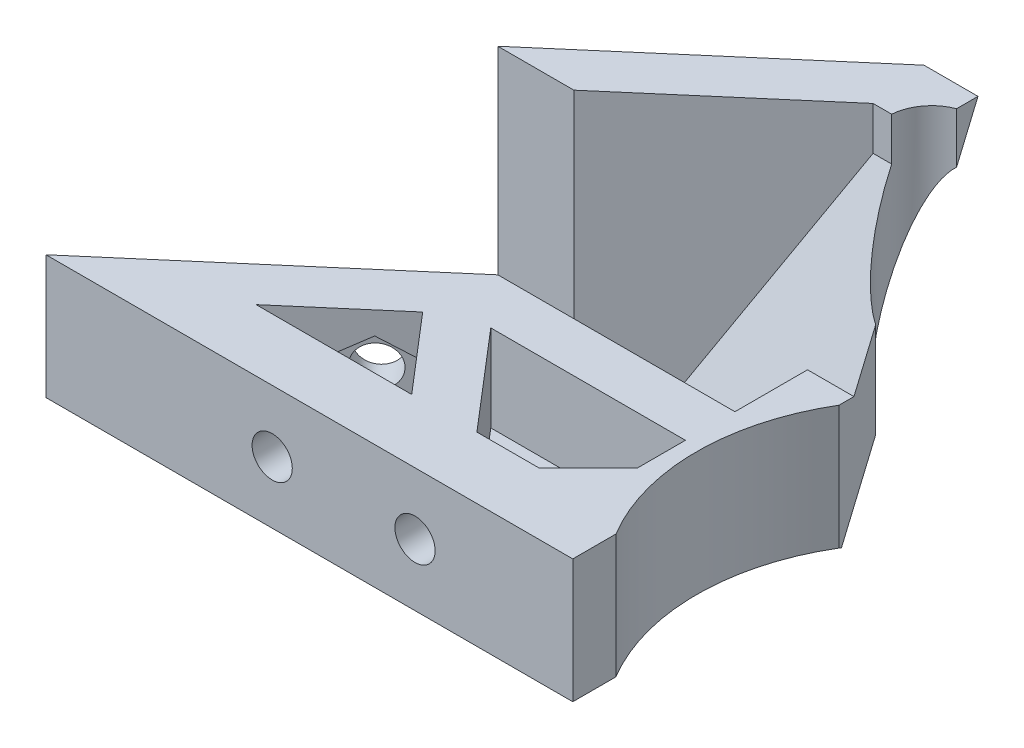
SolidWorks part; units mm, degrees
ref_plane "Alzado" through (0, 0, 0) normal (0, 0, 1) x (1, 0, 0)
ref_plane "Planta" through (0, 0, 0) normal (0, 1, 0) x (1, 0, 0)
ref_plane "Vista lateral" through (0, 0, 0) normal (1, 0, 0) x (0, 0, -1)
sketch "Croquis1" plane through (0, 0, 0) normal (0, 1, 0) x (1, 0, 0)
  line L0 (0, 20) -> (0, -20) construction
  line L1 (-20, 20) -> (20, 20)
  line L2 (-20, 20) -> (-20, -20)
  line L3 (-20, -20) -> (20, -20)
  line L4 (20, 20) -> (20, -20)
  line L5 (-20, 20) -> (20, -20) construction
  line L6 (-20, -20) -> (20, 20) construction
  line L7 (-20, -4.25) -> (-30, -7.25)
  line L8 (-30, -7.25) -> (-30, -15.25)
  line L9 (-30, -15.25) -> (30, -15.25)
  line L10 (20, -4.25) -> (30, -7.25)
  line L11 (30, -7.25) -> (30, -15.25)
  circle A0 centre (-15, 15) radius 2.125
  circle A1 centre (15, 15) radius 2.125
  circle A4 centre (0, 0) radius 15.25
  circle A5 centre (-15, -15) radius 2.125 [skipped]
  circle A6 centre (15, -15) radius 2.125 [skipped]
  point P0 (0, 0)
  point P25 (0, -15.25)
  dimension "D3" = 4.25
  dimension "D7" = 30.5
  dimension "D1" = 40
  dimension "D2" = 40
  dimension "D4" = 5
  dimension "D5" = 2
  dimension "D8" = 8
  dimension "D9" = 10
  dimension "D10" = 15.25
  dimension "D12" = 3
  dimension "D6" = 2
extrude "Soporte caja reductora" add sketch "Croquis1" against normal blind 20
sketch "Croquis3" plane through (0, 0, 15.25) normal (0, 0, 1) x (1, 0, 0)
  line L3 (-20, -20) -> (-20, 0) construction
  circle A0 centre (-23.5, -10) radius 2.125
  circle A1 centre (23.5, -10) radius 2.125
  dimension "D1" = 4.25
  dimension "D2" = 3.5
extrude "Cortar-Extruir1" cut sketch "Croquis3" against normal through all
fillet "Redondeo1" radius 5 2 edges at (-20, -10, -20) (20, -10, -20)
sketch "Sketch1" plane through (0, 0, 0) normal (0, 1, 0) x (1, 0, 0)
  line L0 (15, 20) -> (30, 20)
  line L1 (30, 20) -> (30, 8)
  line L2 (30, 8) -> (25.5, 8)
  line L4 (25.5, 8) -> (25.5, 15)
  line L5 (25.5, 15) -> (20, 15)
  circle A0 centre (15, 15) radius 5
  arc M37 (20, 15) -> (15, 20) centre (15, 15) ccw
  dimension "D1" = 12
  dimension "D2" = 5.5
extrude "Boss-Extrude1" add sketch "Sketch1" along direction (0, 1, 0) on the side against the normal up to surface (20 mm away) contours L5 L4 L2 L1 L0 M37
sketch "Sketch2" plane through (0, 0, -20) normal (0, 0, -1) x (-1, 0, 0)
  line L1 (-20, -20) -> (-20, 0) construction
  circle A0 centre (-22.75, -10) radius 1.625
  dimension "D1" = 3.25
  dimension "D2" = 2.75
extrude "Cut-Extrude1" cut sketch "Sketch2" against normal up to next
sketch "Sketch3" plane through (0, 0, -15) normal (0, 0, 1) x (1, 0, 0)
  line L1 (20, -11.5877) -> (22.75, -13.1754)
  line L2 (22.75, -13.1754) -> (25.5, -11.5877)
  line L3 (25.5, -11.5877) -> (25.5, -8.4123)
  line L4 (25.5, -8.4123) -> (22.75, -6.8246)
  line L5 (22.75, -6.8246) -> (20, -8.4123)
  line L6 (20, -8.4123) -> (20, -11.5877)
  circle A0 centre (22.75, -10) radius 2.75 construction
  dimension "D1" = 5.5
extrude "Cut-Extrude2" cut sketch "Sketch3" against normal blind 2
sketch "Sketch4" plane through (25.5, 0, 0) normal (-1, 0, 0) x (0, 0, 1)
  line L5 (-15, -8.4123) -> (-15, 0) construction
  line L6 (-20, 0) -> (-8, 0) construction
  circle A0 centre (-12.25, -10) radius 1.625
  dimension "D1" = 2.75
  dimension "D2" = 3.25
  dimension "D3" = 10
extrude "Cut-Extrude3" cut sketch "Sketch4" against normal through all
sketch "Sketch5" plane through (30, 0, 0) normal (1, 0, 0) x (0, 0, -1)
  line L1 (15, -11.5877) -> (15, -8.4123)
  line L2 (15, -8.4123) -> (12.25, -6.8246)
  line L3 (12.25, -6.8246) -> (9.5, -8.4123)
  line L4 (9.5, -8.4123) -> (9.5, -11.5877)
  line L5 (9.5, -11.5877) -> (12.25, -13.1754)
  line L6 (12.25, -13.1754) -> (15, -11.5877)
  circle A0 centre (12.25, -10) radius 2.75 construction
  dimension "D1" = 5.5
extrude "Cut-Extrude4" cut sketch "Sketch5" along normal blind 2 from surface
sketch "Croquis6" plane through (0, 0, 0) normal (0, 1, 0) x (1, 0, 0)
  line L0 (-20, -20) -> (20, -20) construction
  line L1 (-15.25, 0) -> (15.25, 0)
  line L2 (-15.25, 0) -> (-15.25, -20)
  line L3 (-15.25, -20) -> (15.25, -20)
  line L4 (15.25, 0) -> (15.25, -20)
  line L6 (-20, -20) -> (20, -20)
  line L7 (-20, -20) -> (-20, -15.25)
  line L8 (-20, -15.25) -> (20, -15.25)
  line L9 (20, -20) -> (20, -15.25)
  circle A0 centre (0, 0) radius 15.25 construction
  circle M5 centre (0, 0) radius 15.25
  line M14 (-20, -15.25) -> (-20, -20)
  line M15 (-20, -20) -> (20, -20)
  line M16 (20, -20) -> (20, -15.25)
extrude "Cortar-Extruir17" cut sketch "Croquis6" against normal through all contours L8 L2 L4 M15 | L8 L2 M14 M15 | L2 L8 M5 | L8 L4 M5 | L8 L4 M15 M16
mirror "Simetría1" about plane through (0, 0, 0) normal (0, 1, 0) of bodies 111
sketch "Croquis7" plane through (0, 0, -20) normal (0, 0, -1) x (-1, 0, 0)
  line L1 (-30, 0) -> (30, 0)
  line L2 (-30, 0) -> (-30, -20)
  line L3 (-30, -20) -> (30, -20)
  line L4 (30, 0) -> (30, -20)
extrude "Cortar-Extruir18" cut sketch "Croquis7" against normal through all
sketch "Croquis8" plane through (0, 20, 0) normal (0, 1, 0) x (1, 0, 0)
  line L3 (-15, 20) -> (30, 20) construction
  line L4 (-11.0405, 13.9391) -> (-10.3152, 11.2321)
  line L5 (10.8174, 13.8793) -> (10.3152, 11.2321)
  line L59 (10.8174, 13.8793) -> (11.9787, 20)
  line L60 (-11.0405, 13.9391) -> (-12.6645, 20)
  line L61 (11.9787, 20) -> (-12.6645, 20)
  circle A0 centre (0, 0) radius 15.25
extrude "Saliente-Extruir2" add sketch "Croquis8" along normal blind 49
sketch "Croquis9" plane through (0, 69, 0) normal (0, 1, 0) x (1, 0, 0)
  line L0 (-20, 0) -> (20, 0)
  line L1 (-20, 15) -> (-20, -4.25) construction
  line L2 (20, 15) -> (20, -4.25) construction
  line L3 (-20, 0) -> (-20, 15)
  line L4 (-15, 20) -> (12.6645, 20)
  line L5 (12.6645, 20) -> (20, 13.9368)
  line L6 (20, 13.9368) -> (20, 0)
  line L7 (20, 0) -> (20.1759, -0.147)
  line L8 (-14.75, 0) -> (-14.75, -15.25)
  line L9 (-15.25, -15.25) -> (-30, -15.25)
  line L10 (-30, -15.25) -> (-30, -7.25)
  line L11 (-30, -7.25) -> (-20, -4.25)
  line L12 (-20, -4.25) -> (-20, 0)
  line L13 (-14.75, -15.25) -> (-15.25, -15.25)
  line L14 (-14.75, -15.25) -> (0, -15.25)
  line L15 (0, -15.25) -> (0, -14.75)
  circle A0 centre (0, 0) radius 14.75
  circle A1 centre (-15, 15) radius 5
  dimension "D1" = 29.5
extrude "Soporte motor" add sketch "Croquis9" against normal blind 15 from offset 15 offset against normal yes
sketch "Croquis12" plane through (0, 0, 15.25) normal (0, 0, 1) x (1, 0, 0)
  line L1 (0, 54) -> (-30, 54) construction
  line L2 (-20, 39) -> (-20, 54) construction
  circle A0 centre (-23.5, 46.5) radius 2.125
  dimension "D3" = 4.25
  dimension "D1" = 7.5
  dimension "D2" = 3.5
extrude "Agujeros de sujecion a base" cut sketch "Croquis12" against normal through all
sketch "Croquis13" plane through (0, 0, 15.25) normal (0, 0, 1) x (1, 0, 0)
  line L1 (-20, 44.4793) -> (-20, 48.5207)
  line L2 (-20, 48.5207) -> (-23.5, 50.5415)
  line L3 (-23.5, 50.5415) -> (-27, 48.5207)
  line L4 (-27, 48.5207) -> (-27, 44.4793)
  line L5 (-27, 44.4793) -> (-23.5, 42.4585)
  line L6 (-23.5, 42.4585) -> (-20, 44.4793)
  circle A0 centre (-23.5, 46.5) radius 3.5 construction
  dimension "D1" = 7
extrude "Tuerca Agujero de sujecion a base" cut sketch "Croquis13" against normal blind 10 from offset 4 offset against normal yes
sketch "Croquis10" plane through (0, 69, 0) normal (0, 1, 0) x (1, 0, 0)
  line L0 (-10.3152, 11.2321) -> (-9.8079, 9.3388)
  line L1 (10.3152, 11.2321) -> (9.4813, 8.1201)
  circle A0 centre (0, 0) radius 14.75
  circle A1 centre (0, 0) radius 15.25
  arc M2 (-10.3152, 11.2321) -> (10.3152, 11.2321) centre (0, 0) cw
extrude "Saliente-Extruir4" add sketch "Croquis10" against normal up to surface (15 mm away) contours A0 L1 L0 M2
sketch "Croquis11" plane through (0, 0, 0) normal (0, -1, 0) x (1, 0, 0)
  line L0 (0, 0) -> (0, -12.6937) construction
  line L1 (15, -20) -> (30, -20)
  line L2 (30, -20) -> (30, 15.25)
  line L3 (30, 15.25) -> (15.25, 15.25)
  line L4 (15.25, 0) -> (15.25, 15.25) construction
  line L5 (15.25, 15.25) -> (30, 15.25) construction
  line L6 (15.25, 15.25) -> (15.25, 4.25)
  line L7 (15.25, 4.25) -> (20, 4.25)
  line L8 (20, 4.25) -> (20, -15)
  circle A0 centre (0, 0) radius 22.5
  circle A1 centre (-15, -15) radius 5
  circle A2 centre (15, -15) radius 5
  line M8 (-15, -20) -> (30, -20)
  line M9 (30, -20) -> (30, -8)
  line M10 (30, -8) -> (25.5, -8)
  line M11 (25.5, -8) -> (25.5, -15)
  line M12 (25.5, -15) -> (20, -15)
  line M14 (20, 4.25) -> (30, 7.25)
  line M15 (30, 7.25) -> (30, 15.25)
  line M16 (30, 15.25) -> (15.25, 15.25)
  line M17 (15.25, 15.25) -> (15.25, 0)
  dimension "D1" = 45
extrude "Cortar-Extruir19" cut sketch "Croquis11" against normal blind 25 contours A0 L3 L7 M14 M17 | A0 M14 M15 M16 | A2 M12 M8 M9 M10 M11
mirror "Simetría2"
sketch "Croquis14" plane through (0, 0, 15.25) normal (0, 0, 1) x (1, 0, 0)
  line L1 (-30, 20) -> (20, 20)
  line L2 (-30, 20) -> (-30, 138)
  line L3 (-30, 138) -> (20, 138)
  line L4 (20, 20) -> (20, 138)
extrude "Cortar-Extruir22" cut sketch "Croquis14" against normal through all
sketch "Croquis15" plane through (0, 0, 0) normal (0, -1, 0) x (1, 0, 0)
  line L0 (-30, 7.25) -> (-30, 15.25) construction
  line L1 (-20, 4.25) -> (-30, 4.25)
  line L2 (-20, 4.25) -> (-20, 11.25)
  line L3 (-20, 11.25) -> (-30, 11.25)
  line L4 (-30, 4.25) -> (-30, 11.25)
  line L5 (-30, 15.25) -> (-15.25, 15.25) construction
  dimension "D1" = 4
extrude "Cortar-Extruir23" cut sketch "Croquis15" against normal through all
sketch "Croquis16" plane through (0, 0, 0) normal (0, -1, 0) x (1, 0, 0)
  line L0 (-15.25, 0) -> (-15.25, 15.25) construction
  line L1 (-30, 15.25) -> (-15.25, 15.25)
  line L2 (-30, 15.25) -> (-30, 12.75)
  line L3 (-20, 12.75) -> (-15.25, 12.75)
  line L4 (-15.25, 15.25) -> (-15.25, 12.75)
  line L5 (-30, 12.75) -> (-30, 11.25)
  line L6 (-30, 11.25) -> (-20, 11.25)
  line L7 (-20, 11.25) -> (-30, 11.25) construction
  line L8 (-20, -15) -> (-20, 11.25) construction
  line L9 (-20, 11.25) -> (-20, 12.75)
  dimension "D1" = 2.5
extrude "Cortar-Extruir24" cut sketch "Croquis16" against normal through all
sketch "Croquis18" plane through (0, 0, -20) normal (0, 0, -1) x (-1, 0, 0)
  line L0 (20, 0) -> (20, 20) construction
  line L1 (-20, 0) -> (20, 0)
  line L2 (-20, 0) -> (-20, 10)
  line L3 (-20, 10) -> (20, 10)
  line L4 (20, 0) -> (20, 10)
  line L5 (15, 20) -> (-15, 20) construction
  dimension "D1" = 10
extrude "Cortar-Extruir25" cut sketch "Croquis18" against normal through all
sketch "Croquis19" plane through (0, 20, 0) normal (0, 1, 0) x (1, 0, 0)
  line L0 (-20, -12.75) -> (-34, -12.75)
  line L1 (-34, -12.75) -> (-34, -7.75)
  line L2 (-34, -7.75) -> (-24, -7.75)
  line L3 (-24, -7.75) -> (-20, -3.75)
  line L4 (-20, 15) -> (-20, -12.75) construction
  line L5 (-20, -3.75) -> (-20, -12.75)
  dimension "D1" = 5
  dimension "D2" = 4
  dimension "D3" = 4
  dimension "D4" = 10
extrude "Saliente-Extruir5" add sketch "Croquis19" against normal up to surface (10 mm away) up to face at (15, 10, -12.875)
sketch "Croquis20" plane through (0, 0, 7.75) normal (0, 0, -1) x (-1, 0, 0)
  circle A0 centre (29, 15) radius 1
  dimension "D1" = 2
extrude "Cortar-Extruir26" cut sketch "Croquis20" against normal through all
sketch "Croquis21" plane through (20, 0, 0) normal (1, 0, 0) x (0, 0, -1)
  line L1 (20, 20) -> (20, 10) construction
  circle A0 centre (4.75, 15) radius 1.625
  dimension "D1" = 3.25
  dimension "D2" = 15.25
extrude "Cortar-Extruir27" cut sketch "Croquis21" against normal up to next
sketch "Croquis22" plane through (0, 10, 0) normal (0, -1, 0) x (1, 0, 0)
  circle A0 centre (-15, -15) radius 2.125
  circle A1 centre (15, -15) radius 2.125
  circle A2 centre (15, -15) radius 1
  circle A3 centre (-15, -15) radius 1
  dimension "D1" = 2
extrude "Saliente-Extruir6" add sketch "Croquis22" against normal blind 10
sketch "Croquis23" plane through (0, 0, -20) normal (0, 0, -1) x (-1, 0, 0)
  circle A0 centre (0, 15) radius 1.625
  dimension "D1" = 3.25
extrude "Cortar-Extruir28" cut sketch "Croquis23" against normal through all
sketch "Croquis24" plane through (0, 0, -20) normal (0, 0, -1) x (-1, 0, 0)
  line L1 (1.5877, 12.25) -> (3.1754, 15)
  line L2 (3.1754, 15) -> (1.5877, 17.75)
  line L3 (1.5877, 17.75) -> (-1.5877, 17.75)
  line L4 (-1.5877, 17.75) -> (-3.1754, 15)
  line L5 (-3.1754, 15) -> (-1.5877, 12.25)
  line L6 (-1.5877, 12.25) -> (1.5877, 12.25)
  circle A0 centre (0, 15) radius 2.75 construction
  dimension "D1" = 5.5
extrude "Cortar-Extruir29" cut sketch "Croquis24" against normal blind 10 from offset 3 offset against normal yes
sketch "Croquis26" plane through (0, 10, 0) normal (0, -1, 0) x (1, 0, 0)
  line L0 (-29, 12.75) -> (-58.825, 12.75)
  line L1 (-58.825, 12.75) -> (-39.1605, -4.1045)
  line L3 (-39.5945, 1.5357) -> (-46.8449, 7.75)
  line L4 (-46.8449, 7.75) -> (-34.2682, 7.75)
  line L5 (-34.2682, 7.75) -> (-39.5945, 1.5357)
  line L7 (-29, 7.75) -> (-35.7321, -0.1045)
  line L8 (-29, 7.75) -> (-29, 12.75)
  line L9 (-34, 7.75) -> (-24, 7.75) construction
  line L10 (-34, 12.75) -> (-15.25, 12.75) construction
  line L11 (-39.1605, -4.1045) -> (-20, -4.1045)
  line L12 (-20, 3.75) -> (-20, -15) construction
  line L13 (-20, -4.1045) -> (-20, -0.1045)
  line L14 (-20, -0.1045) -> (-35.7321, -0.1045)
  dimension "D1" = 4
  dimension "D2" = 4
  dimension "D3" = 4
  dimension "D4" = 29.825
  dimension "D5" = 40.6
extrude "Saliente-Extruir7" add sketch "Croquis26" against normal blind 10
sketch "Croquis27" plane through (0, 0, 12.75) normal (0, 0, 1) x (1, 0, 0)
  line L0 (-29, 16) -> (-29, 14) construction
  line L1 (-46.8449, 20) -> (-46.8449, 10) construction
  circle A0 centre (-40.5449, 15) radius 1.625
  circle A2 centre (-29, 15) radius 1.625
  dimension "D1" = 3.25
  dimension "D2" = 6.3
extrude "Cortar-Extruir30" cut sketch "Croquis27" against normal up to next
sketch "Croquis28" plane through (0, 0, 12.75) normal (0, 0, 1) x (1, 0, 0)
  line L1 (-38.9572, 12.25) -> (-37.3694, 15)
  line L2 (-37.3694, 15) -> (-38.9572, 17.75)
  line L3 (-38.9572, 17.75) -> (-42.1326, 17.75)
  line L4 (-42.1326, 17.75) -> (-43.7203, 15)
  line L5 (-43.7203, 15) -> (-42.1326, 12.25)
  line L6 (-42.1326, 12.25) -> (-38.9572, 12.25)
  line L7 (-27.4123, 12.25) -> (-25.8246, 15)
  line L8 (-25.8246, 15) -> (-27.4123, 17.75)
  line L9 (-27.4123, 17.75) -> (-30.5877, 17.75)
  line L10 (-30.5877, 17.75) -> (-32.1754, 15)
  line L11 (-32.1754, 15) -> (-30.5877, 12.25)
  line L12 (-30.5877, 12.25) -> (-27.4123, 12.25)
  circle A0 centre (-40.5449, 15) radius 2.75 construction
  circle A1 centre (-29, 15) radius 2.75 construction
  dimension "D1" = 5.5
extrude "Cortar-Extruir31" cut sketch "Croquis28" against normal up to next from offset 3 offset against normal yes
sketch "Croquis29" plane through (-18.6128, 0, -21.716) normal (-0.6508, 0, -0.7593) x (-0.7593, 0, 0.6508)
  line L2 (31.0624, 20) -> (31.0624, 10) construction
  circle A0 centre (33.8124, 15) radius 1.625
  dimension "D2" = 3.25
  dimension "D1" = 2.75
extrude "Cortar-Extruir32" cut sketch "Croquis29" against normal up to next
sketch "Croquis31" plane through (-18.6128, 0, -21.716) normal (-0.6508, 0, -0.7593) x (-0.7593, 0, 0.6508)
  line L1 (36.5624, 16.5877) -> (33.8124, 18.1754)
  line L2 (33.8124, 18.1754) -> (31.0624, 16.5877)
  line L3 (31.0624, 16.5877) -> (31.0624, 13.4123)
  line L4 (31.0624, 13.4123) -> (33.8124, 11.8246)
  line L5 (33.8124, 11.8246) -> (36.5624, 13.4123)
  line L6 (36.5624, 13.4123) -> (36.5624, 16.5877)
  circle A0 centre (33.8124, 15) radius 2.75 construction
  dimension "D1" = 5.5
extrude "Cortar-Extruir33" cut sketch "Croquis31" against normal up to next from offset 2.5 offset against normal yes
sketch "Croquis35" plane through (0, 20, 0) normal (0, 1, 0) x (1, 0, 0)
  line L0 (-15, 20) -> (15, 20) construction
  line L1 (10.3896, 0) -> (23.695, 0)
  line L2 (10.3896, 0) -> (10.3896, -6.8269)
  line L3 (10.3896, -6.8269) -> (23.695, -6.8269)
  line L4 (23.695, 0) -> (23.695, -6.8269)
  dimension "D1" = 20
extrude "Cortar-Extruir34" cut sketch "Croquis35" against normal through all both and the other way through all
sketch "Croquis36" plane through (20, 0, 0) normal (1, 0, 0) x (0, 0, -1)
  line L1 (7.5, 16.5877) -> (4.75, 18.1754)
  line L2 (4.75, 18.1754) -> (2, 16.5877)
  line L3 (2, 16.5877) -> (2, 13.4123)
  line L4 (2, 13.4123) -> (4.75, 11.8246)
  line L5 (4.75, 11.8246) -> (7.5, 13.4123)
  line L6 (7.5, 13.4123) -> (7.5, 16.5877)
  circle A0 centre (4.75, 15) radius 2.75 construction
  dimension "D1" = 5.5
extrude "Cortar-Extruir35" cut sketch "Croquis36" against normal blind 10 from offset 3 offset against normal yes
sketch "Croquis37" plane through (0, 10, 0) normal (0, -1, 0) x (1, 0, 0)
  line L0 (-39.1605, -4.1045) -> (-20.6149, -20)
  line L1 (-20.6149, -20) -> (-15, -20)
  line L2 (-33.014, -4.1045) -> (-19.5581, -15.6376)
  line L3 (-39.1605, -4.1045) -> (-20, -4.1045) construction
  line L4 (-19.5581, -15.6376) -> (-15, -20)
  line L5 (-58.825, 12.75) -> (-39.1605, -4.1045) construction
  line L6 (-39.5945, 1.5357) -> (-46.8449, 7.75) construction
  line L7 (-39.1605, -4.1045) -> (-33.014, -4.1045)
extrude "Saliente-Extruir8" add sketch "Croquis37" against normal blind 10
sketch "Croquis38" plane through (0, 10, 0) normal (0, -1, 0) x (1, 0, 0)
  line L0 (-58.825, 12.75) -> (-38.825, 12.75)
  line L1 (-58.825, 12.75) -> (-15.25, 12.75) construction
  line L2 (-38.825, 12.75) -> (-38.825, 9.75)
  line L3 (-38.825, 9.75) -> (-55.3248, 9.75)
  line L4 (-58.825, 12.75) -> (-20.6149, -20) construction
  line L5 (-55.3248, 9.75) -> (-58.825, 12.75)
  dimension "D1" = 3
  dimension "D2" = 20
extrude "Saliente-Extruir9" add sketch "Croquis38" along normal blind 13
sketch "Croquis39" plane through (0, 10, 0) normal (0, -1, 0) x (1, 0, 0)
  line L0 (-38.825, 9.75) -> (-38.825, 7.75)
  line L1 (-46.8449, 7.75) -> (-34.2682, 7.75) construction
  line L3 (-55.3248, 9.75) -> (-20.6149, -20) construction
  line L4 (-52.9914, 7.75) -> (-55.3248, 9.75)
  line L5 (-55.3248, 9.75) -> (-38.825, 9.75)
  line L6 (-52.9914, 7.75) -> (-50.658, 5.75)
  line L7 (-50.658, 5.75) -> (-38.825, 5.75)
  line L8 (-38.825, 5.75) -> (-38.825, 7.75)
  dimension "D1" = 2
extrude "Saliente-Extruir10" add sketch "Croquis39" along normal blind 3
mirror "Simetría3" of bodies 142
sketch "Croquis40" plane through (0, 0, -20) normal (0, 0, -1) x (-1, 0, 0)
  line L1 (-30.8963, 20) -> (75.6873, 20)
  line L2 (-30.8963, 20) -> (-30.8963, -27.3915)
  line L3 (-30.8963, -27.3915) -> (75.6873, -27.3915)
  line L4 (75.6873, 20) -> (75.6873, -27.3915)
extrude "Cortar-Extruir36" cut sketch "Croquis40" against normal through all both and the other way through all
sketch "Croquis41" plane through (0, 0, -20) normal (0, 0, -1) x (-1, 0, 0)
  line L1 (38.825, 30) -> (63.3839, 30)
  line L2 (38.825, 30) -> (38.825, 48.2062)
  line L3 (38.825, 48.2062) -> (63.3839, 48.2062)
  line L4 (63.3839, 30) -> (63.3839, 48.2062)
extrude "Cortar-Extruir37" cut sketch "Croquis41" against normal through all both and the other way through all
sketch "Croquis42" plane through (0, 20, 0) normal (0, -1, 0) x (1, 0, 0)
  line L0 (-58.825, 12.75) -> (-15.25, 12.75) construction
  line L1 (-16.25, 12.75) -> (23.5436, 12.75)
  line L2 (-16.25, 12.75) -> (-16.25, -23.8027)
  line L3 (-16.25, -23.8027) -> (23.5436, -23.8027)
  line L4 (23.5436, 12.75) -> (23.5436, -23.8027)
  line L5 (-15.25, 12.75) -> (-15.25, 0) construction
  dimension "D1" = 1
extrude "Cortar-Extruir38" cut sketch "Croquis42" against normal through all both and the other way through all
sketch "Croquis43" plane through (0, 20, 0) normal (0, -1, 0) x (1, 0, 0)
  line L0 (-46.8449, 7.75) -> (-19.5619, 7.75)
  line L1 (-19.5619, 7.75) -> (-19.5619, -16.3714)
  line L2 (-19.5619, -16.3714) -> (-46.8449, 7.75)
extrude "Saliente-Extruir11" add sketch "Croquis43" against normal blind 3
sketch "Croquis44" plane through (0, 30, 0) normal (0, 1, 0) x (1, 0, 0)
  line L0 (-58.825, -12.75) -> (-16.25, -12.75) construction
  line L1 (-16.25, -12.75) -> (-16.25, 20) construction
  circle A0 centre (-1.25, -0.25) radius 17.5
  dimension "D1" = 35
  dimension "D2" = 12.5
  dimension "D3" = 15
extrude "Cortar-Extruir39" cut sketch "Croquis44" against normal through all both and the other way through all
sketch "Croquis45" plane through (0, 30, 0) normal (0, 1, 0) x (1, 0, 0)
  line L0 (-33.014, 4.1045) -> (-39.1605, 4.1045)
  line L1 (-58.825, -12.75) -> (-20.6149, 20) construction
  line L2 (-39.1605, 4.1045) -> (-20.6149, 20)
  line L3 (-20.6149, 20) -> (-16.25, 20)
  line L4 (-16.25, 20) -> (-16.25, 15.2649)
  line L5 (-33.014, 4.1045) -> (-19.993, 15.2649)
  line L6 (-19.993, 15.2649) -> (-16.25, 15.2649)
extrude "Saliente-Extruir12" add sketch "Croquis45" along normal blind 16
sketch "Croquis46" plane through (-16.25, 0, 0) normal (1, 0, 0) x (0, 0, -1)
  line L0 (9, 20) -> (20, 46)
  line L1 (-12.75, 20) -> (20, 20) construction
  line L2 (20, 46) -> (20, 20)
  line L3 (20, 20) -> (9, 20)
  dimension "D1" = 11
extrude "Cortar-Extruir40" cut sketch "Croquis46" against normal through all
sketch "Croquis47" plane through (0, -0.1932, -0.4567) normal (0, -0.3896, -0.921) x (-1, 0, 0)
  line L5 (16.25, 21.8341) -> (33.4488, 21.9261)
  line L6 (33.4488, 21.9261) -> (22.7201, 45.5265)
  line L7 (33.4488, 21.9261) -> (20.6149, 50.1573) construction
  line L8 (22.7201, 45.5265) -> (16.25, 45.5265)
  line L9 (16.25, 50.1573) -> (16.25, 38.0047) construction
  line L10 (16.25, 45.5265) -> (16.25, 21.8341)
extrude "Saliente-Extruir14" add sketch "Croquis47" against normal blind 3
sketch "Croquis48" plane through (0, 20, 0) normal (0, -1, 0) x (1, 0, 0)
  circle A0 centre (-1.25, 0.25) radius 17.5
extrude "Cortar-Extruir41" cut sketch "Croquis48" against normal through all both and the other way through all
sketch "Croquis49" plane through (0, 20, 0) normal (0, -1, 0) x (1, 0, 0)
  line L0 (-16.25, -20) -> (-16.25, -8.9642) construction
  line L1 (-16.25, -20) -> (-20.6149, -20) construction
  circle A0 centre (-15, -15) radius 3.5
  dimension "D1" = 7
  dimension "D2" = 1.25
  dimension "D3" = 5
extrude "Cortar-Extruir42" cut sketch "Croquis49" against normal through all
